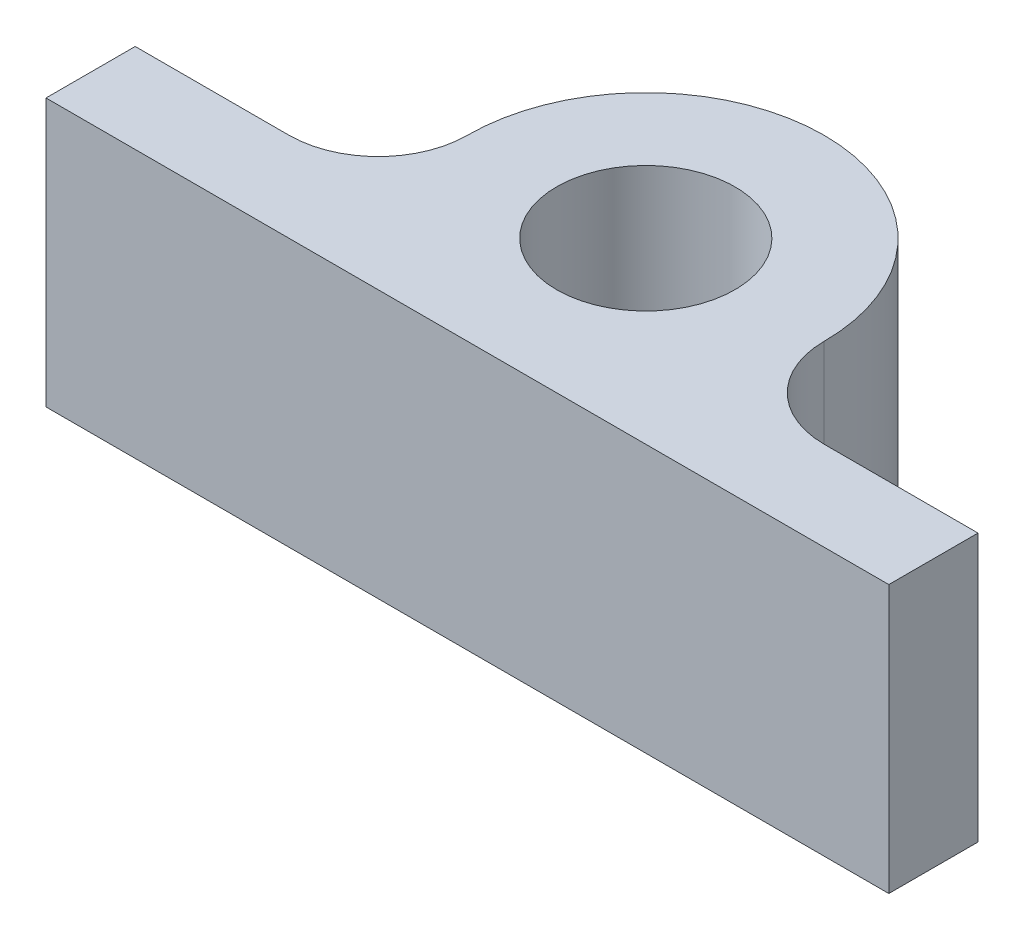
SolidWorks part; units mm, degrees
material "AISI 1020"
ref_plane "Front Plane" through (0, 0, 0) normal (0, 0, 1) x (1, 0, 0)
ref_plane "Top Plane" through (0, 0, 0) normal (0, 1, 0) x (1, 0, 0)
ref_plane "Right Plane" through (0, 0, 0) normal (1, 0, 0) x (0, 0, -1)
sketch "Sketch1" plane through (0, 0, 0) normal (0, 1, 0) x (1, 0, 0)
  line L0 (-1087.63, -12.7) -> (-38.1, -12.7) construction
  line L1 (-10.567, -25.4) -> (-78.8525, -25.4) construction
  line L2 (-25.4, -1025.4) -> (-25.4, -12.7) construction
  line L3 (-60, -25.4) -> (60, -25.4)
  line L4 (-60, -25.4) -> (-60, -12.7)
  line L5 (-60, -12.7) -> (-38.1, -12.7)
  line L6 (60, -25.4) -> (60, -12.7)
  line L7 (25.4, 0) -> (25.4, 17.7271) construction
  line L8 (-25.4, 0) -> (-25.4, 19.4283) construction
  line L9 (0, -12.7) -> (69.1941, -12.7) construction
  line L10 (0, -12.7) -> (60, -12.7) construction
  line L11 (60, -12.7) -> (38.1, -12.7)
  arc A0 (0, -25.4) -> (-25.4, 0) centre (0, 0) ccw construction
  circle A1 centre (0, 0) radius 12.7
  arc A2 (-38.1, -12.7) -> (-25.4, 0) centre (-38.1, 0) ccw
  arc A3 (25.4, 0) -> (38.1, -12.7) centre (38.1, 0) ccw
  arc A4 (25.4, 0) -> (-25.4, 0) centre (0, 0) ccw
  point P4 (21.997, -12.7)
  point P5 (0, -25.4)
  point P14 (-21.997, -12.7)
  point P15 (-25.4, 0)
  point P16 (25.4, 0)
  point P18 (-25.4, -12.7)
  point P21 (-38.1, -12.7)
  point P23 (-38.1, 0)
  point P26 (25.4, -12.7)
  point P30 (38.1, 0)
  point P31 (38.1, -12.7)
  dimension "D1" = 50.8
  dimension "D2" = 25.4
  dimension "D10" = 25.4
  dimension "D3" = 12.7
  dimension "D4" = 60
  dimension "D5" = 60
  dimension "D6" = 12.7
  dimension "D7" = 12.7
  dimension "D8" = 12.7
  dimension "D9" = 12.7
extrude "Boss-Extrude1" add sketch "Sketch1" along normal blind 38.1 contours A3 A4 A2 L5 L4 L3 L6 L11 A1
ref_plane "Plane1" through (0, 0, 0) normal (1, 0, 0) x (0, 0, -1)
